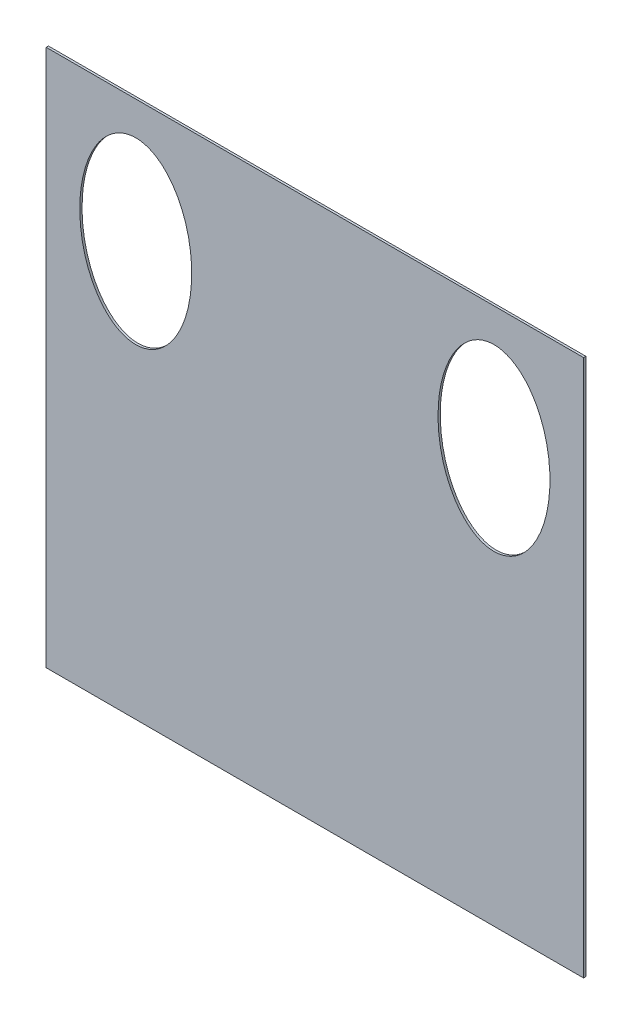
SolidWorks part; units mm, degrees
material "PVC Rigid"
ref_plane "Front Plane" through (0, 0, 0) normal (0, 0, 1) x (1, 0, 0)
ref_plane "Top Plane" through (0, 0, 0) normal (0, 1, 0) x (1, 0, 0)
ref_plane "Right Plane" through (0, 0, 0) normal (1, 0, 0) x (0, 0, -1)
sketch "Sketch1" plane through (0, 0, 0) normal (0, 0, 1) x (1, 0, 0)
  line L1 (-183.8876, 299.1322) -> (425.7124, 299.1322)
  line L2 (-183.8876, 299.1322) -> (-183.8876, -310.4678)
  line L3 (-183.8876, -310.4678) -> (425.7124, -310.4678)
  line L4 (425.7124, 299.1322) -> (425.7124, -310.4678)
  dimension "D1" = 609.6
  dimension "D2" = 609.6
extrude "Boss-Extrude1" add sketch "Sketch1" along normal blind 2.54
sketch "Sketch2" plane through (0, 0, 2.54) normal (0, 0, 1) x (1, 0, 0)
  line L0 (120.9124, 299.1322) -> (120.9124, -310.4678) construction
  line L1 (425.7124, 299.1322) -> (-183.8876, 299.1322) construction
  line L2 (-183.8876, -310.4678) -> (425.7124, -310.4678) construction
  line L3 (-183.8876, 299.1322) -> (-183.8876, -310.4678) construction
  ellipse E0 centre (-82.2876, 159.4322) end of major axis (-82.2876, 57.8322) minor radius 63.5
  ellipse E1 centre (324.1124, 159.4322) end of major axis (324.1124, 57.8322) minor radius 63.5
  dimension "D1" = 203.2
  dimension "D2" = 127
  dimension "D3" = 101.6
  dimension "D4" = 139.7
extrude "Cut-Extrude1" cut sketch "Sketch2" against normal through all
